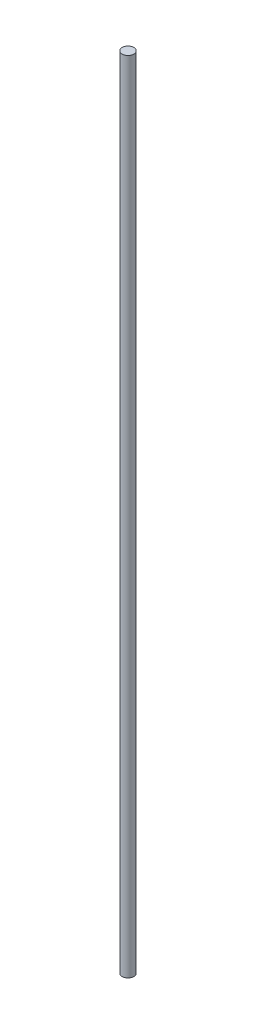
SolidWorks part; units mm, degrees
ref_plane "Plan de face" through (0, 0, 0) normal (0, 0, 1) x (1, 0, 0)
ref_plane "Plan de dessus" through (0, 0, 0) normal (0, 1, 0) x (1, 0, 0)
ref_plane "Plan de droite" through (0, 0, 0) normal (1, 0, 0) x (0, 0, -1)
sketch "Esquisse1" plane through (0, 0, 0) normal (0, 1, 0) x (1, 0, 0)
  circle A0 centre (0, 0) radius 1.5
  dimension "D1" = 3
extrude "Boss.-Extru.1" add sketch "Esquisse1" along normal blind 205.8
